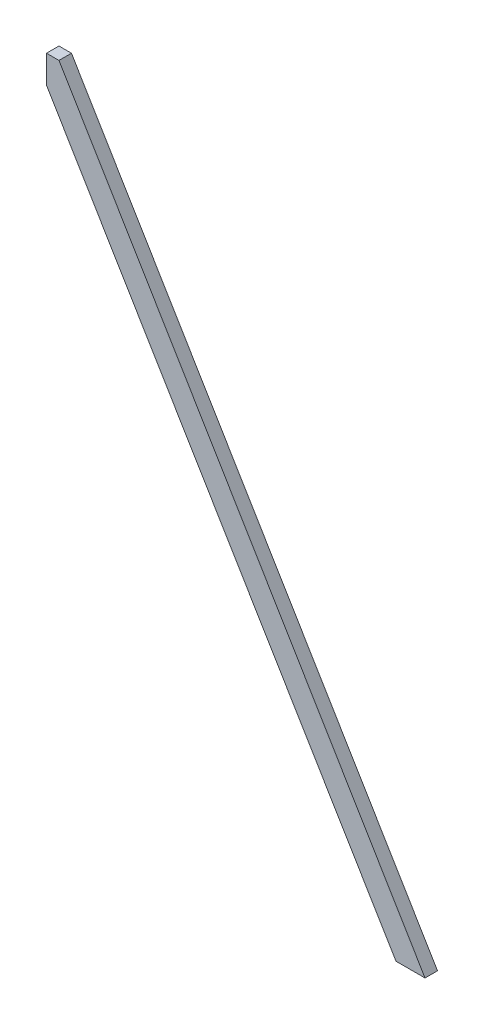
SolidWorks part; units mm, degrees
material "Cedar"
ref_plane "Front Plane" through (0, 0, 0) normal (0, 0, 1) x (1, 0, 0)
ref_plane "Top Plane" through (0, 0, 0) normal (0, 1, 0) x (1, 0, 0)
ref_plane "Right Plane" through (0, 0, 0) normal (1, 0, 0) x (0, 0, -1)
ref_plane "Plane1" through (0, 0, 0) normal (-0.7071, 0, 0.7071) x (0.7071, 0, 0.7071)
sketch "Sketch1" plane through (0, 0, 0) normal (0, 0, 1) x (1, 0, 0)
  line L0 (-18.796, 0) -> (-18.796, 965.517) construction
  line L1 (-18.796, 0) -> (559.054, 0) construction
  line L2 (559.054, 0) -> (-18.796, 965.517)
  line L3 (-18.796, 891.3263) -> (514.6518, 0)
  line L4 (-18.796, 965.517) -> (-18.796, 891.3263)
  line L5 (514.6518, 0) -> (559.054, 0)
  dimension "D1" = 30.9
  dimension "D2" = 577.85
  dimension "D3" = 38.1
  dimension "D4" = 18.796
extrude "Boss-Extrude1" add sketch "Sketch1" against normal blind 19.05
sketch "Sketch2" plane through (0, 0, 0) normal (0, 0, 1) x (1, 0, 0)
  line L0 (-18.796, 965.517) -> (-18.796, 933.6868)
  line L1 (-18.796, 965.517) -> (-18.796, 891.3263) construction
  line L2 (-18.796, 933.6868) -> (0.254, 933.6868)
  line L3 (559.054, 0) -> (-18.796, 965.517) construction
  line L4 (0.254, 933.6868) -> (-18.796, 965.517)
  line L5 (0.254, 933.6868) -> (0.254, 859.496) construction
  line L6 (-18.796, 891.3263) -> (514.6518, 0) construction
  dimension "D1" = 19.05
extrude "Cut-Extrude1" cut sketch "Sketch2" against normal through all
